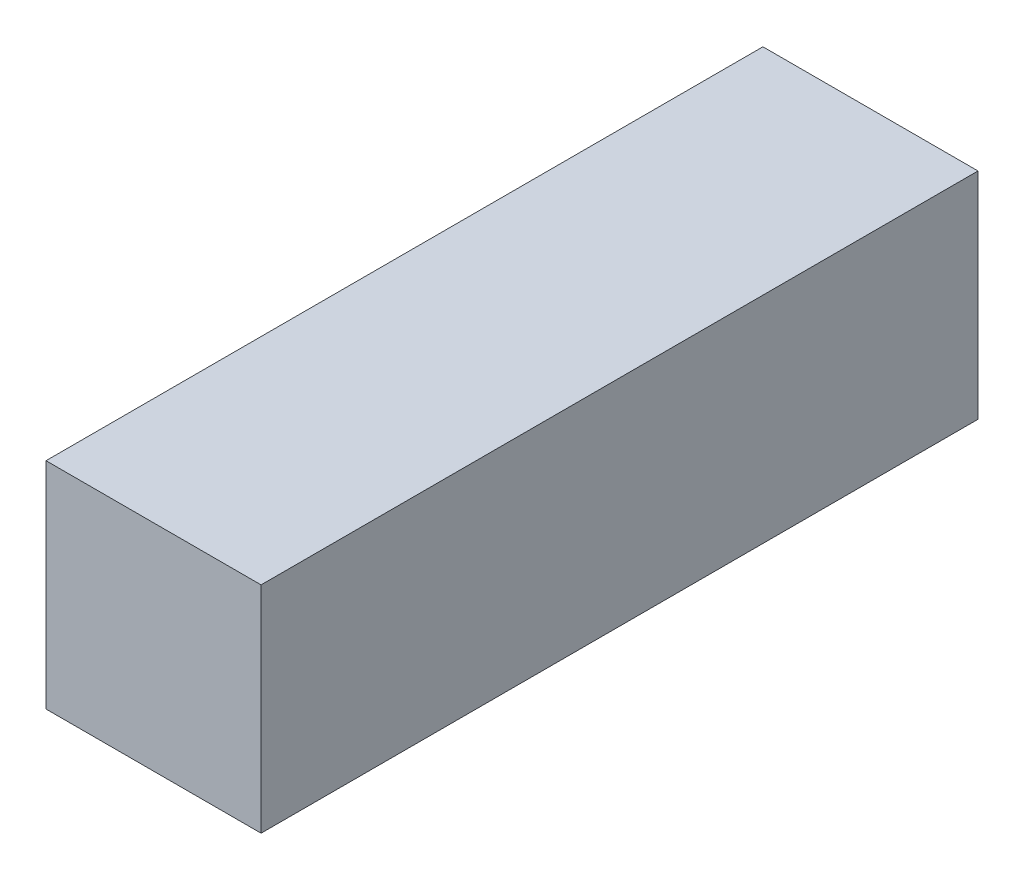
SolidWorks part; units mm, degrees
ref_plane "Front Plane" through (0, 0, 0) normal (0, 0, 1) x (1, 0, 0)
ref_plane "Top Plane" through (0, 0, 0) normal (0, 1, 0) x (1, 0, 0)
ref_plane "Right Plane" through (0, 0, 0) normal (1, 0, 0) x (0, 0, -1)
sketch "Sketch1" plane through (0, 0, 0) normal (0, 0, 1) x (1, 0, 0)
  line L1 (1.905, -1.905) -> (-1.905, -1.905)
  line L2 (1.905, -1.905) -> (1.905, 1.905)
  line L3 (1.905, 1.905) -> (-1.905, 1.905)
  line L4 (-1.905, -1.905) -> (-1.905, 1.905)
  line L5 (1.905, -1.905) -> (-1.905, 1.905) construction
  line L6 (1.905, 1.905) -> (-1.905, -1.905) construction
  point P0 (0, 0)
  dimension "D1" = 3.81
  dimension "D2" = 3.81
extrude "Boss-Extrude1" add sketch "Sketch1" along normal blind 12.7
